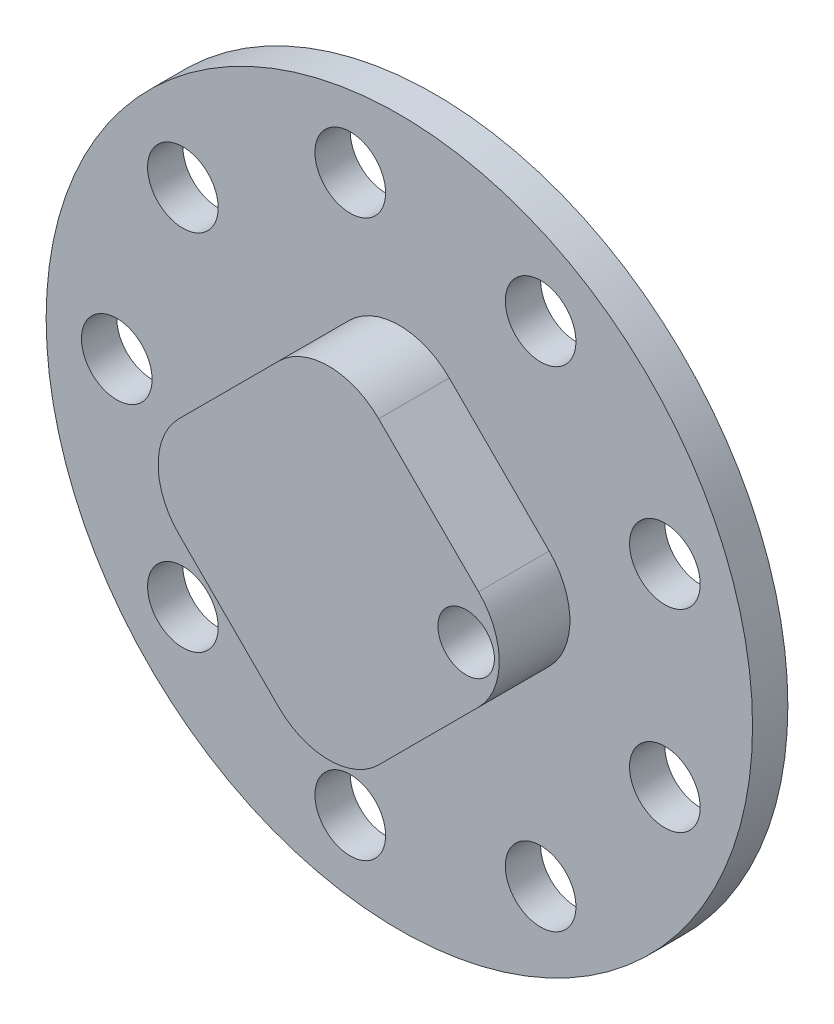
SolidWorks part; units mm, degrees
ref_plane "Přední rovina" through (0, 0, 0) normal (0, 0, 1) x (1, 0, 0)
ref_plane "Horní rovina" through (0, 0, 0) normal (0, 1, 0) x (1, 0, 0)
ref_plane "Pravá rovina" through (0, 0, 0) normal (1, 0, 0) x (0, 0, -1)
sketch "Skica1" plane through (0, 0, 0) normal (0, 0, 1) x (1, 0, 0)
  circle A0 centre (0, 0) radius 50
  dimension "D1" = 100
extrude "Vysunout1" add sketch "Skica1" along normal blind 5
sketch "Skica2" plane through (0, 0, 5) normal (0, 0, 1) x (1, 0, 0)
  line L0 (0.8264, 47.586) -> (0, 50) construction
  line L1 (0, 50) -> (0, -50) construction
  line L2 (50, 0) -> (-50, 0) construction
  line L3 (-28.2843, 0) -> (28.2843, 0) construction
  line L5 (0, 28.2843) -> (-28.2843, 0)
  line L6 (-28.2843, 0) -> (0, -28.2843)
  line L7 (0, -28.2843) -> (28.2843, 0)
  line L8 (0, 28.2843) -> (0, -28.2843) construction
  line L9 (28.2843, 0) -> (0, 28.2843)
  circle A0 centre (0, 0) radius 40 construction
  circle A1 centre (0, 0) radius 50 construction
  circle A2 centre (0, 0) radius 20 construction
  point P19 (0, 0)
  dimension "D1" = 80
  dimension "D2" = 40
  dimension "D3" = 40
sketch "Skica3" plane through (0, 0, 5) normal (0, 0, 1) x (1, 0, 0)
  line L0 (50, 0) -> (-50, 0) construction
  circle A0 centre (-40, 0) radius 5
  circle A1 centre (0, 0) radius 40 construction
  dimension "D1" = 10
extrude "Odebrat vysunutím1" cut sketch "Skica3" against normal through all
pattern_circular "Kruhové pole1" count 9 over 360 about axis through (0, 0, 0) along (0, 0, 1) of "Odebrat vysunutím1"
extrude "Vysunout2" add sketch "Skica2" along normal blind 10
fillet "Zaoblit2" radius 10 4 edges at (-28.2843, 0, 10) (0, -28.2843, 10) (28.2843, 0, 10) (0, 28.2843, 10)
sketch "Skica5" plane through (0, 0, 15) normal (0, 0, 1) x (1, 0, 0)
  circle A0 centre (19.4604, 0) radius 4
  dimension "D1" = 8
extrude "Odebrat vysunutím2" cut sketch "Skica5" against normal up to next
